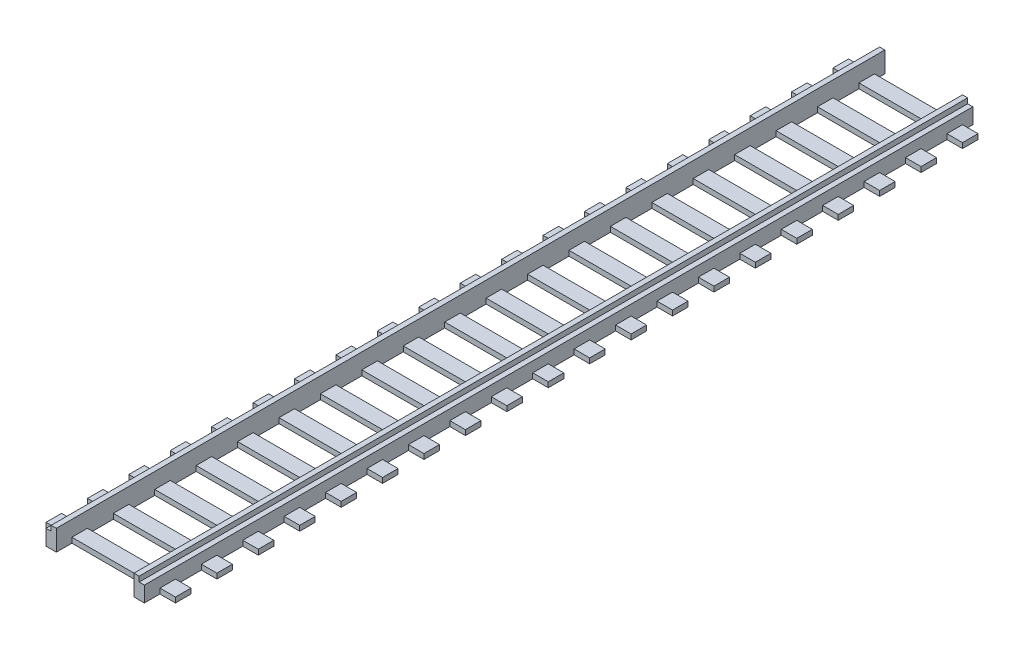
SolidWorks part; units mm, degrees
ref_plane "Front Plane" through (0, 0, 0) normal (0, 0, 1) x (1, 0, 0)
ref_plane "Top Plane" through (0, 0, 0) normal (0, 1, 0) x (1, 0, 0)
ref_plane "Right Plane" through (0, 0, 0) normal (1, 0, 0) x (0, 0, -1)
sketch "Sketch1" plane through (0, 0, 0) normal (0, 1, 0) x (1, 0, 0)
  line L1 (-43.6876, 71.25) -> (-42.6876, 71.25)
  line L2 (-43.6876, 71.25) -> (-43.6876, -88.75)
  line L3 (-43.6876, -88.75) -> (-42.6876, -88.75)
  line L4 (-42.6876, 71.25) -> (-42.6876, -88.75)
  line L5 (-27.6876, 71.25) -> (-26.6876, 71.25)
  line L6 (-27.6876, 71.25) -> (-27.6876, -88.75)
  line L7 (-27.6876, -88.75) -> (-26.6876, -88.75)
  line L8 (-26.6876, 71.25) -> (-26.6876, -88.75)
  dimension "D1" = 160
  dimension "D2" = 1
  dimension "D3" = 1
  dimension "D4" = 15
extrude "Boss-Extrude1" add sketch "Sketch1" along normal blind 4
sketch "Sketch2" plane through (0, 0, 0) normal (0, -1, 0) x (1, 0, 0)
  line L0 (-43.6876, -71.25) -> (-43.6876, 88.75) construction
  line L1 (-43.6876, -71.25) -> (-43.6876, 88.75)
  line L2 (-44.6876, -71.25) -> (-44.6876, 88.75)
  line L3 (-43.6876, -71.25) -> (-44.6876, -71.25)
  line L4 (-43.6876, 88.75) -> (-44.6876, 88.75)
  line L5 (-26.6876, 88.75) -> (-26.6876, -71.25) construction
  line L6 (-26.6876, 88.75) -> (-26.6876, -71.25)
  line L7 (-25.6876, 88.75) -> (-25.6876, -71.25)
  line L8 (-26.6876, 88.75) -> (-25.6876, 88.75)
  line L9 (-26.6876, -71.25) -> (-25.6876, -71.25)
  dimension "D1" = 1
  dimension "D2" = 1
extrude "Boss-Extrude2" add sketch "Sketch2" against normal blind 3
sketch "Sketch3" plane through (0, 0, 0) normal (0, -1, 0) x (1, 0, 0)
  line L0 (-44.6876, 88.75) -> (-44.6876, -71.25) construction
  line L1 (-47.6876, 85.75) -> (-22.6876, 85.75)
  line L2 (-47.6876, 85.75) -> (-47.6876, 82.75)
  line L3 (-47.6876, 82.75) -> (-22.6876, 82.75)
  line L4 (-22.6876, 85.75) -> (-22.6876, 82.75)
  line L5 (-25.6876, -71.25) -> (-25.6876, 88.75) construction
  line L6 (-47.6876, 77.75) -> (-47.6876, 74.75)
  line L7 (-47.6876, 77.75) -> (-22.6876, 77.75)
  line L8 (-22.6876, 77.75) -> (-22.6876, 74.75)
  line L9 (-47.6876, 74.75) -> (-22.6876, 74.75)
  line L10 (-47.6876, 69.75) -> (-47.6876, 66.75)
  line L11 (-47.6876, 69.75) -> (-22.6876, 69.75)
  line L12 (-22.6876, 69.75) -> (-22.6876, 66.75)
  line L13 (-47.6876, 66.75) -> (-22.6876, 66.75)
  line L14 (-47.6876, 61.75) -> (-47.6876, 58.75)
  line L15 (-47.6876, 61.75) -> (-22.6876, 61.75)
  line L16 (-22.6876, 61.75) -> (-22.6876, 58.75)
  line L17 (-47.6876, 58.75) -> (-22.6876, 58.75)
  line L18 (-47.6876, 53.75) -> (-47.6876, 50.75)
  line L19 (-47.6876, 53.75) -> (-22.6876, 53.75)
  line L20 (-22.6876, 53.75) -> (-22.6876, 50.75)
  line L21 (-47.6876, 50.75) -> (-22.6876, 50.75)
  line L22 (-47.6876, 45.75) -> (-47.6876, 42.75)
  line L23 (-47.6876, 45.75) -> (-22.6876, 45.75)
  line L24 (-22.6876, 45.75) -> (-22.6876, 42.75)
  line L25 (-47.6876, 42.75) -> (-22.6876, 42.75)
  line L26 (-47.6876, 37.75) -> (-47.6876, 34.75)
  line L27 (-47.6876, 37.75) -> (-22.6876, 37.75)
  line L28 (-22.6876, 37.75) -> (-22.6876, 34.75)
  line L29 (-47.6876, 34.75) -> (-22.6876, 34.75)
  line L30 (-47.6876, 29.75) -> (-47.6876, 26.75)
  line L31 (-47.6876, 29.75) -> (-22.6876, 29.75)
  line L32 (-22.6876, 29.75) -> (-22.6876, 26.75)
  line L33 (-47.6876, 26.75) -> (-22.6876, 26.75)
  line L34 (-47.6876, 21.75) -> (-47.6876, 18.75)
  line L35 (-47.6876, 21.75) -> (-22.6876, 21.75)
  line L36 (-22.6876, 21.75) -> (-22.6876, 18.75)
  line L37 (-47.6876, 18.75) -> (-22.6876, 18.75)
  line L38 (-47.6876, 13.75) -> (-47.6876, 10.75)
  line L39 (-47.6876, 13.75) -> (-22.6876, 13.75)
  line L40 (-22.6876, 13.75) -> (-22.6876, 10.75)
  line L41 (-47.6876, 10.75) -> (-22.6876, 10.75)
  line L42 (-47.6876, 5.75) -> (-47.6876, 2.75)
  line L43 (-47.6876, 5.75) -> (-22.6876, 5.75)
  line L44 (-22.6876, 5.75) -> (-22.6876, 2.75)
  line L45 (-47.6876, 2.75) -> (-22.6876, 2.75)
  line L46 (-47.6876, -2.25) -> (-47.6876, -5.25)
  line L47 (-47.6876, -2.25) -> (-22.6876, -2.25)
  line L48 (-22.6876, -2.25) -> (-22.6876, -5.25)
  line L49 (-47.6876, -5.25) -> (-22.6876, -5.25)
  line L50 (-47.6876, -10.25) -> (-47.6876, -13.25)
  line L51 (-47.6876, -10.25) -> (-22.6876, -10.25)
  line L52 (-22.6876, -10.25) -> (-22.6876, -13.25)
  line L53 (-47.6876, -13.25) -> (-22.6876, -13.25)
  line L54 (-47.6876, -18.25) -> (-47.6876, -21.25)
  line L55 (-47.6876, -18.25) -> (-22.6876, -18.25)
  line L56 (-22.6876, -18.25) -> (-22.6876, -21.25)
  line L57 (-47.6876, -21.25) -> (-22.6876, -21.25)
  line L58 (-47.6876, -26.25) -> (-47.6876, -29.25)
  line L59 (-47.6876, -26.25) -> (-22.6876, -26.25)
  line L60 (-22.6876, -26.25) -> (-22.6876, -29.25)
  line L61 (-47.6876, -29.25) -> (-22.6876, -29.25)
  line L62 (-47.6876, -34.25) -> (-47.6876, -37.25)
  line L63 (-47.6876, -34.25) -> (-22.6876, -34.25)
  line L64 (-22.6876, -34.25) -> (-22.6876, -37.25)
  line L65 (-47.6876, -37.25) -> (-22.6876, -37.25)
  line L66 (-47.6876, -42.25) -> (-47.6876, -45.25)
  line L67 (-47.6876, -42.25) -> (-22.6876, -42.25)
  line L68 (-22.6876, -42.25) -> (-22.6876, -45.25)
  line L69 (-47.6876, -45.25) -> (-22.6876, -45.25)
  line L70 (-47.6876, -50.25) -> (-47.6876, -53.25)
  line L71 (-47.6876, -50.25) -> (-22.6876, -50.25)
  line L72 (-22.6876, -50.25) -> (-22.6876, -53.25)
  line L73 (-47.6876, -53.25) -> (-22.6876, -53.25)
  line L74 (-47.6876, -58.25) -> (-47.6876, -61.25)
  line L75 (-47.6876, -58.25) -> (-22.6876, -58.25)
  line L76 (-22.6876, -58.25) -> (-22.6876, -61.25)
  line L77 (-47.6876, -61.25) -> (-22.6876, -61.25)
  line L78 (-47.6876, -66.25) -> (-47.6876, -69.25)
  line L79 (-47.6876, -66.25) -> (-22.6876, -66.25)
  line L80 (-22.6876, -66.25) -> (-22.6876, -69.25)
  line L81 (-47.6876, -69.25) -> (-22.6876, -69.25)
  dimension "D1" = 3
  dimension "D2" = 3
  dimension "D3" = 3
  dimension "D4" = 3
  dimension "D5" = 20
extrude "Boss-Extrude3" add sketch "Sketch3" against normal blind 1
